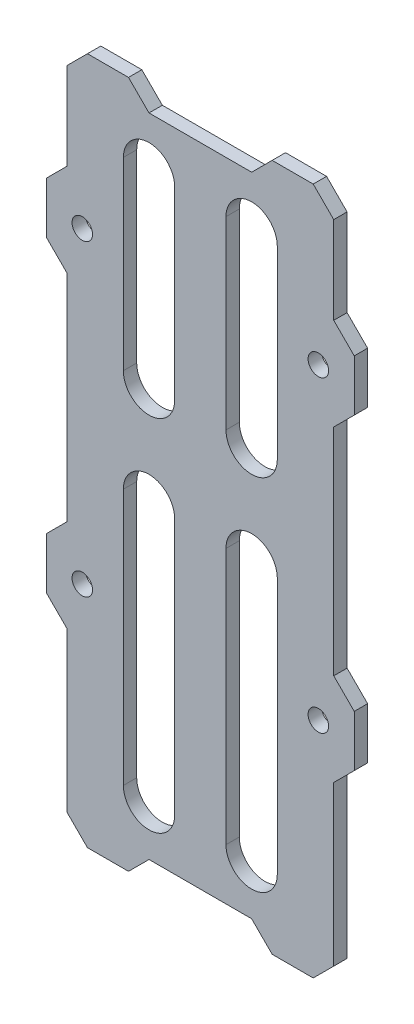
SolidWorks part; units mm, degrees
material "Thornel Mat VMA"
ref_plane "Přední rovina" through (0, 0, 0) normal (0, 0, 1) x (1, 0, 0)
ref_plane "Horní rovina" through (0, 0, 0) normal (0, 1, 0) x (1, 0, 0)
ref_plane "Pravá rovina" through (0, 0, 0) normal (1, 0, 0) x (0, 0, -1)
sketch "Skica1" plane through (0, 0, 0) normal (0, 0, 1) x (1, 0, 0)
  line L1 (-15, -37) -> (15, -37)
  line L2 (-15, -37) -> (-15, 30)
  line L3 (-15, 30) -> (15, 30)
  line L4 (15, -37) -> (15, 30)
  line L5 (-15, -37) -> (15, 30) construction
  line L6 (-15, 30) -> (15, -37) construction
  line L7 (11.5, -15) -> (-11.5, -15) construction
  line L8 (11.5, -15) -> (11.5, 15) construction
  line L9 (11.5, 15) -> (-11.5, 15) construction
  line L10 (-11.5, -15) -> (-11.5, 15) construction
  line L11 (11.5, -15) -> (-11.5, 15) construction
  line L12 (11.5, 15) -> (-11.5, -15) construction
  circle A0 centre (-11.5, 15) radius 1
  circle A1 centre (-11.5, -15) radius 1
  circle A2 centre (11.5, -15) radius 1
  circle A3 centre (11.5, 15) radius 1
  point P0 (0, -3.5)
  point P5 (0, 0)
  dimension "D5" = 2
  dimension "D1" = 30
  dimension "D2" = 67
  dimension "D3" = 30
  dimension "D4" = 23
  dimension "D6" = 30
extrude "Přidat vysunutím1" add sketch "Skica1" along normal blind 1.3
sketch "Skica2" plane through (0, 0, 1.3) normal (0, 0, 1) x (1, 0, 0)
  line L0 (0, 30) -> (0, -37) construction
  line L1 (15, 30) -> (-15, 30) construction
  line L2 (-15, -37) -> (15, -37) construction
  line L3 (-11.5, 15) -> (-15, 15) construction
  line L4 (-15, 30) -> (-15, -37) construction
  line L5 (-11.5, -15) -> (-15, -15) construction
  line L6 (-15, 17.5) -> (-15, 12.5)
  line L7 (-15, 12.5) -> (-13, 10.5)
  line L8 (-13, 10.5) -> (-13, -10.5)
  line L9 (-13, -10.5) -> (-15, -12.5)
  line L10 (-15, -12.5) -> (-15, -17.5)
  line L11 (-15, -17.5) -> (-13, -19.5)
  line L12 (-13, -19.5) -> (-13, -37)
  line L13 (-15, 17.5) -> (-13, 19.5)
  line L14 (-13, 19.5) -> (-13, 30)
  line L15 (-7, 30) -> (-5, 28)
  line L16 (-5, 28) -> (5, 28)
  line L17 (-7, -37) -> (-5, -35)
  line L18 (-5, -35) -> (5, -35)
  line L19 (-5, 23) -> (-5, 5) construction
  line L20 (-2.5, 23) -> (-2.5, 5)
  line L21 (-7.5, 23) -> (-7.5, 5)
  line L22 (-5, -5) -> (-5, -30) construction
  line L23 (-2.5, -5) -> (-2.5, -30)
  line L24 (-7.5, -5) -> (-7.5, -30)
  line L25 (0, -35) -> (0, -40.5371)
  line L26 (21.4956, -40.5371) -> (-21.4956, -40.5371)
  line L27 (-21.4956, -40.5371) -> (-21.4956, 36.1748)
  line L28 (-21.4956, 36.1748) -> (21.4956, 36.1748)
  line L29 (0, 36.1748) -> (0, 28)
  line L30 (-13, 30) -> (-7, 30)
  line L31 (-13, -37) -> (-7, -37)
  line L32 (11.5, -15) -> (15, -15) construction
  line L33 (11.5, 15) -> (15, 15) construction
  line L34 (13, -37) -> (7, -37)
  line L35 (13, 30) -> (7, 30)
  line L36 (21.4956, -40.5371) -> (21.4956, 36.1748)
  line L37 (7, -37) -> (5, -35)
  line L38 (7, 30) -> (5, 28)
  line L39 (13, 19.5) -> (13, 30)
  line L40 (15, 17.5) -> (13, 19.5)
  line L41 (13, -19.5) -> (13, -37)
  line L42 (15, -17.5) -> (13, -19.5)
  line L43 (15, -12.5) -> (15, -17.5)
  line L44 (13, -10.5) -> (15, -12.5)
  line L45 (13, 10.5) -> (13, -10.5)
  line L46 (15, 12.5) -> (13, 10.5)
  line L47 (15, 17.5) -> (15, 12.5)
  line L48 (5, -5) -> (5, -30) construction
  line L49 (2.5, -5) -> (2.5, -30)
  line L50 (7.5, -5) -> (7.5, -30)
  line L51 (5, 23) -> (5, 5) construction
  line L52 (2.5, 23) -> (2.5, 5)
  line L53 (7.5, 23) -> (7.5, 5)
  arc A0 (-2.5, 23) -> (-7.5, 23) centre (-5, 23) ccw
  arc A1 (-7.5, 5) -> (-2.5, 5) centre (-5, 5) ccw
  arc A2 (-2.5, -5) -> (-7.5, -5) centre (-5, -5) ccw
  arc A3 (-7.5, -30) -> (-2.5, -30) centre (-5, -30) ccw
  arc A4 (2.5, -5) -> (7.5, -5) centre (5, -5) cw
  arc A5 (7.5, -30) -> (2.5, -30) centre (5, -30) cw
  arc A6 (2.5, 23) -> (7.5, 23) centre (5, 23) cw
  arc A7 (7.5, 5) -> (2.5, 5) centre (5, 5) cw
  point P32 (-5, 14)
  point P37 (-5, -17.5)
  point P71 (5, -17.5)
  point P78 (5, 14)
  line M3 (15, -37) -> (15, 30)
  line M4 (15, 30) -> (-15, 30)
  line M5 (-15, 30) -> (-15, -37)
  line M6 (-15, -37) -> (15, -37)
  dimension "D2" = 2.5
  dimension "D1" = 5
  dimension "D3" = 5
  dimension "D4" = 25
  dimension "D5" = 18
  dimension "D6" = 2
  dimension "D7" = 135
  dimension "D8" = 5
  dimension "D9" = 5
  dimension "D10" = 2.5
  dimension "D11" = 5
  dimension "D12" = 2.5
  dimension "D13" = 45
  dimension "D14" = 2
  dimension "D15" = 5
  dimension "D16" = 2
extrude "Odebrat vysunutím1" cut sketch "Skica2" against normal blind 1.3 contours L29 L28 L27 L26 L25 M6 M5 M4 | L26 L36 L28 L29 L25 M4 M3 M6 | L40 L39 M3 M4 | L46 L45 L44 M3 | L42 L41 M3 M6 | L37 L18 L25 M6 | L25 L18 L17 M6 | L12 L11 M5 M6 | L9 L8 L7 M5 | L13 L14 M4 M5 | L38 L29 L16 M4 | L29 L15 L16 M4 | L21 A1 L20 A0 | A7 L53 A6 L52 | A5 L50 A4 L49 | L24 A3 L23 A2
chamfer "Zkosení1" distance 2 angle 45 4 edges at (13, -37, 0.65) (-13, -37, 0.65) (13, 30, 0.65) (-13, 30, 0.65)
scale "Scala1" scale about centroid uniform scaling yes scale factor 0.64
